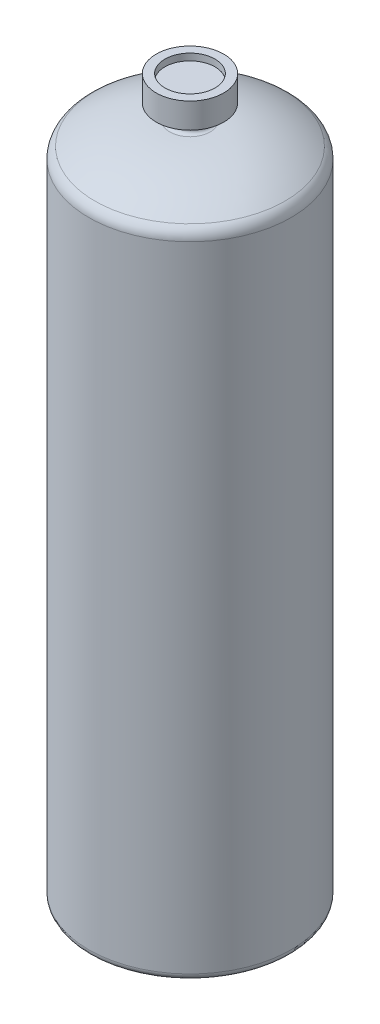
SolidWorks part; units mm, degrees
ref_plane "Front Plane" through (0, 0, 0) normal (0, 0, 1) x (1, 0, 0)
ref_plane "Top Plane" through (0, 0, 0) normal (0, 1, 0) x (1, 0, 0)
ref_plane "Right Plane" through (0, 0, 0) normal (1, 0, 0) x (0, 0, -1)
sketch "Sketch1" plane through (0, 0, 0) normal (0, 0, 1) x (1, 0, 0)
  line L0 (0, 0) -> (0, 269.24) construction
  line L1 (0, 0) -> (-38.1, 0)
  line L2 (-38.1, 0) -> (-38.1, 241.3)
  line L3 (-6.35, 255.27) -> (-6.35, 259.715)
  line L4 (-6.35, 259.715) -> (-12.7, 259.715)
  line L5 (-12.7, 259.715) -> (-12.7, 269.24)
  line L6 (-12.7, 269.24) -> (0, 269.24)
  line L7 (-7.62, 254) -> (0, 254) construction
  line L8 (0, 0) -> (0, 269.24)
  arc A0 (-38.1, 241.3) -> (-35.8163, 245.5411) centre (-33.02, 241.3) cw
  arc A1 (-35.8163, 245.5411) -> (-7.62, 254) centre (-7.62, 202.7767) cw
  arc A2 (-7.62, 254) -> (-6.35, 255.27) centre (-7.62, 255.27) ccw
  point P11 (-7.62, 162.8271)
  point P16 (-7.62, 162.8271)
  point P17 (-41.0611, 154.9713)
  point P18 (-35.7053, 156.9002)
  dimension "D2" = 1.27
  dimension "D9" = 5.08
  dimension "D1" = 241.3
  dimension "D3" = 15.24
  dimension "D4" = 25.4
  dimension "D5" = 12.7
  dimension "D6" = 9.525
  dimension "D7" = 12.7
  dimension "D8" = 76.2
revolve "Revolve1" add sketch "Sketch1" angle 360 about L8
fillet "Fillet1" radius 2.54 1 edges at (0, 0, -38.1)
sketch "Sketch2" plane through (0, 269.24, 0) normal (0, 1, 0) x (1, 0, 0)
  circle A0 centre (0, 0) radius 9.4268
extrude "Cut-Extrude1" cut sketch "Sketch2" against normal blind 2.54
